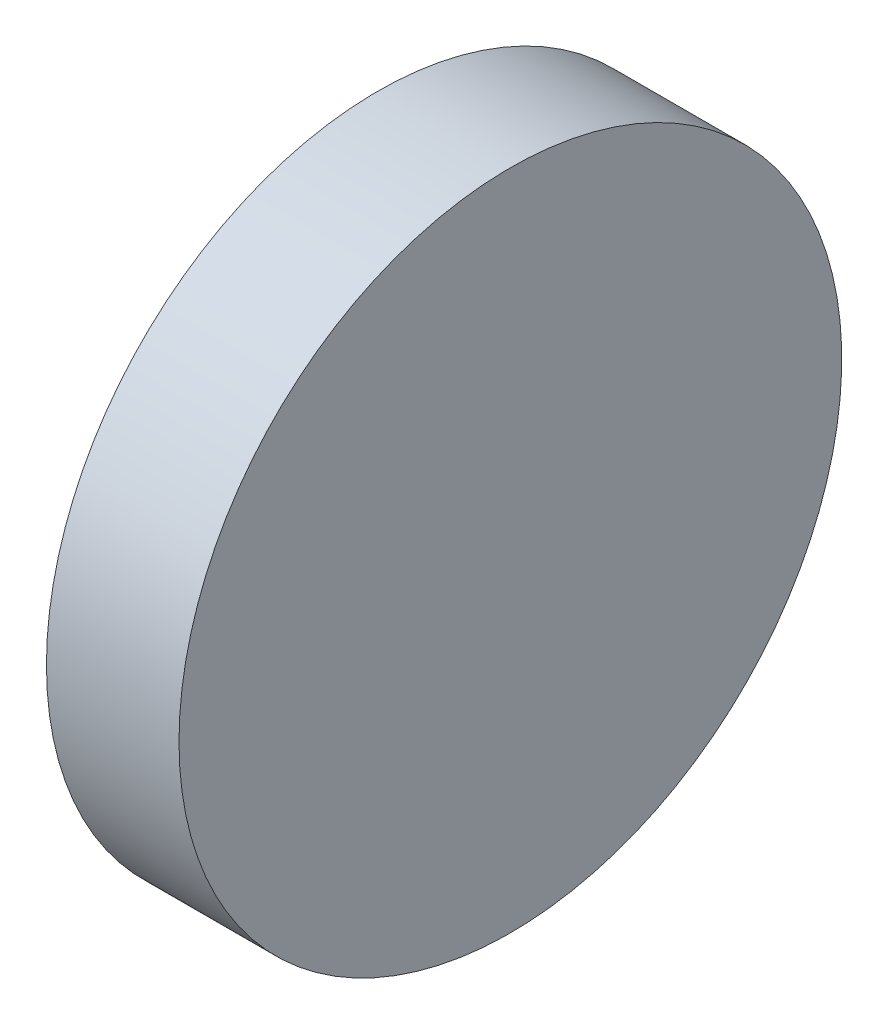
SolidWorks part; units mm, degrees
ref_plane "前视基准面" through (0, 0, 0) normal (0, 0, 1) x (1, 0, 0)
ref_plane "上视基准面" through (0, 0, 0) normal (0, 1, 0) x (1, 0, 0)
ref_plane "右视基准面" through (0, 0, 0) normal (1, 0, 0) x (0, 0, -1)
sketch "草图1" plane through (0, 0, 0) normal (0, 0, 1) x (1, 0, 0)
  line L0 (-3, 12.7) -> (-3, 0)
  line L2 (-3, 12.7) -> (3, 12.7)
  line L3 (-3, 0) -> (3, 0)
  line L4 (3, 12.7) -> (3, 0)
revolve "旋转2" add sketch "草图1" angle 360 about L3
sketch "草图4" plane through (0, 0, 0) normal (0, 0, 1) x (1, 0, 0)
  line L0 (-3, 15) -> (3, 15)
  line L1 (3, 15) -> (3, 12.7)
  line L2 (3, 12.7) -> (-3, 12.7)
  line L3 (3, 12.7) -> (-3, 12.7) construction
  line L4 (-3, 12.7) -> (-3, 15)
  line L5 (0, 12.7) -> (0, 15) construction
  line L6 (-1.6142, 0) -> (1.5903, 0) construction
revolve "旋转3" add sketch "草图4" angle 360 about L6
equation "\"D1@草图4\"=\"D1@草图1\""
